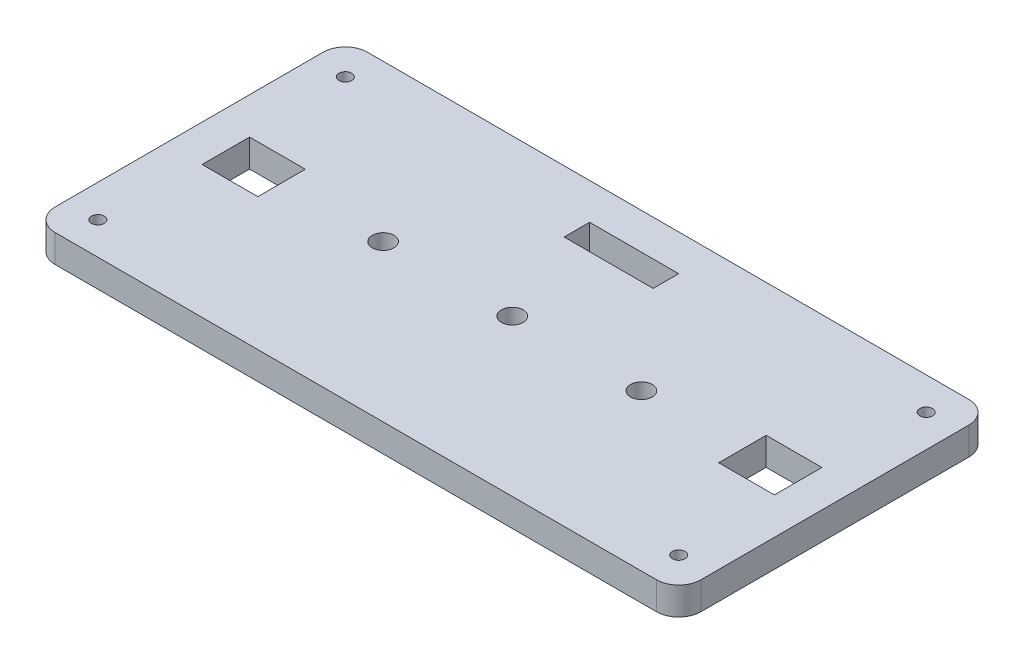
SolidWorks part; units mm, degrees
ref_plane "Front Plane" through (0, 0, 0) normal (0, 0, 1) x (1, 0, 0)
ref_plane "Top Plane" through (0, 0, 0) normal (0, 1, 0) x (1, 0, 0)
ref_plane "Right Plane" through (0, 0, 0) normal (1, 0, 0) x (0, 0, -1)
sketch "Sketch1" plane through (0, 0, 0) normal (0, 1, 0) x (1, 0, 0)
  line L1 (-73.914, -35.7505) -> (73.914, -35.7505)
  line L2 (-73.914, -35.7505) -> (-73.914, 35.7505)
  line L3 (-73.914, 35.7505) -> (73.914, 35.7505)
  line L4 (73.914, -35.7505) -> (73.914, 35.7505)
  line L5 (-73.914, -35.7505) -> (73.914, 35.7505) construction
  line L6 (-73.914, 35.7505) -> (73.914, -35.7505) construction
  point P0 (0, 0)
  dimension "D1" = 147.828
  dimension "D2" = 71.501
extrude "Boss-Extrude1" add sketch "Sketch1" along normal blind 6.35
fillet "Fillet1" radius 5.08 4 edges at (-73.914, 3.175, 35.7505) (73.914, 3.175, 35.7505) (73.914, 3.175, -35.7505) (-73.914, 3.175, -35.7505)
sketch "Sketch2" plane through (0, 6.35, 0) normal (0, 1, 0) x (1, 0, 0)
  line L0 (-59.1312, 0) -> (-73.914, 0) construction
  line L1 (52.7558, 5.4356) -> (65.5066, 5.4356)
  line L2 (52.7558, 5.4356) -> (52.7558, -5.4356)
  line L3 (52.7558, -5.4356) -> (65.5066, -5.4356)
  line L4 (65.5066, 5.4356) -> (65.5066, -5.4356)
  line L5 (-65.5066, 5.4356) -> (-52.7558, 5.4356)
  line L6 (-65.5066, 5.4356) -> (-65.5066, -5.4356)
  line L7 (-65.5066, -5.4356) -> (-52.7558, -5.4356)
  line L8 (-52.7558, 5.4356) -> (-52.7558, -5.4356)
  line L10 (-52.7558, 5.4356) -> (-65.5066, -5.4356) construction
  line L11 (-65.5066, 5.4356) -> (-52.7558, -5.4356) construction
  line L12 (-59.1312, 0) -> (-59.1312, 35.7505) construction
  line L13 (68.834, 35.7505) -> (-68.834, 35.7505) construction
  line L14 (65.5066, 5.4356) -> (52.7558, -5.4356) construction
  line L15 (52.7558, 5.4356) -> (65.5066, -5.4356) construction
  line L16 (59.1312, 0) -> (73.914, 0) construction
  line L17 (73.914, -30.6705) -> (73.914, 30.6705) construction
  line L20 (-73.914, 30.6705) -> (-73.914, -30.6705) construction
  line L21 (59.1312, 0) -> (59.1312, 35.7505) construction
  line L22 (-59.1312, 0) -> (-29.5057, 0) construction
  line L23 (29.6255, 0) -> (-29.5057, 0) construction
  line L24 (29.6255, 0) -> (0.0599, 0) construction
  circle A0 centre (-29.5057, 0) radius 2.4892
  circle A1 centre (29.6255, 0) radius 2.4892
  circle A2 centre (0.0599, 0) radius 2.4892
  point P20 (59.1312, 0)
  point P27 (0, 0)
  dimension "D5" = 4.9784
  dimension "D6" = 4.9784
  dimension "D1" = 12.7508
  dimension "D2" = 12.7508
  dimension "D3" = 10.8712
  dimension "D4" = 10.8712
  dimension "D7" = 14.7828
  dimension "D8" = 35.7505
  dimension "D9" = 14.7828
  dimension "D10" = 35.7505
  dimension "D11" = 29.5656
  dimension "D12" = 29.5656
extrude "Cut-Extrude1" cut sketch "Sketch2" against normal through all
sketch "Sketch3" plane through (0, 6.35, 0) normal (0, 1, 0) x (1, 0, 0)
  line L0 (-67.945, 28.321) -> (-73.914, 28.321) construction
  line L1 (-73.914, 30.6705) -> (-73.914, -30.6705) construction
  line L2 (-66.4845, 29.7815) -> (-66.4845, 35.7505) construction
  line L3 (68.834, 35.7505) -> (-68.834, 35.7505) construction
  line L4 (73.914, 0) -> (-73.914, 0) construction
  line L5 (73.914, -30.6705) -> (73.914, 30.6705) construction
  line L6 (0, 35.7505) -> (0, -35.7505) construction
  line L7 (-68.834, -35.7505) -> (68.834, -35.7505) construction
  circle A0 centre (-66.4845, 28.321) radius 1.4605
  circle A1 centre (66.4845, 28.321) radius 1.4605
  circle A2 centre (66.4845, -28.321) radius 1.4605
  circle A3 centre (-66.4845, -28.321) radius 1.4605
  dimension "D3" = 2.921
  dimension "D1" = 5.969
  dimension "D2" = 5.969
extrude "Cut-Extrude2" cut sketch "Sketch3" against normal through all
sketch "Sketch4" plane through (0, 6.35, 0) normal (0, 1, 0) x (1, 0, 0)
  text T0 "Lock"
  text T1 "Zero"
  text T2 "Ready"
  text T3 "Sending"
  text T4 "  Not \r\nReady"
sketch "Sketch5" plane through (0, 6.35, 0) normal (0, 1, 0) x (1, 0, 0)
  line L1 (-9.6969, 27.4639) -> (10.6947, 27.4639)
  line L2 (-9.6969, 27.4639) -> (-9.6969, 21.6259)
  line L3 (-9.6969, 21.6259) -> (10.6947, 21.6259)
  line L4 (10.6947, 27.4639) -> (10.6947, 21.6259)
extrude "Cut-Extrude3" cut sketch "Sketch5" against normal through all
equation "\"width\"=5.82"
equation "\"D1@Sketch1\"=\"width\""
equation "\"length\"=2.815"
equation "\"D2@Sketch1\"=\"length\""
equation "\"D1@Boss-Extrude1\" = \"material\""
equation "\"material\"= .25"
equation "\"button_width\"= 0.502"
equation "\"D1@Sketch2\"=\"button_width\""
equation "\"D2@Sketch2\"= \"button_width\""
equation "\"button_length\"=0.428"
equation "\"D3@Sketch2\"=\"button_length\""
equation "\"D4@Sketch2\"=\"button_length\" "
equation "\"LED\"=0.196"
equation "\"D5@Sketch2\"=\"LED\""
equation "\"D6@Sketch2\"= \"LED\""
equation "\"D8@Sketch2\"=\"length\" / 2"
equation "\"D7@Sketch2\"=\"width\" / 10"
equation "\"D9@Sketch2\"=\"width\" / 10"
equation "\"D10@Sketch2\"= \"length\" / 2"
equation "\"D11@Sketch2\"=\"width\" / 5"
equation "\"D12@Sketch2\"=\"width\" / 5"
equation "\"screw_position\"=0.235"
equation "\"D1@Sketch3\"=\"screw_position\""
equation "\"D2@Sketch3\"=\"screw_position\""
